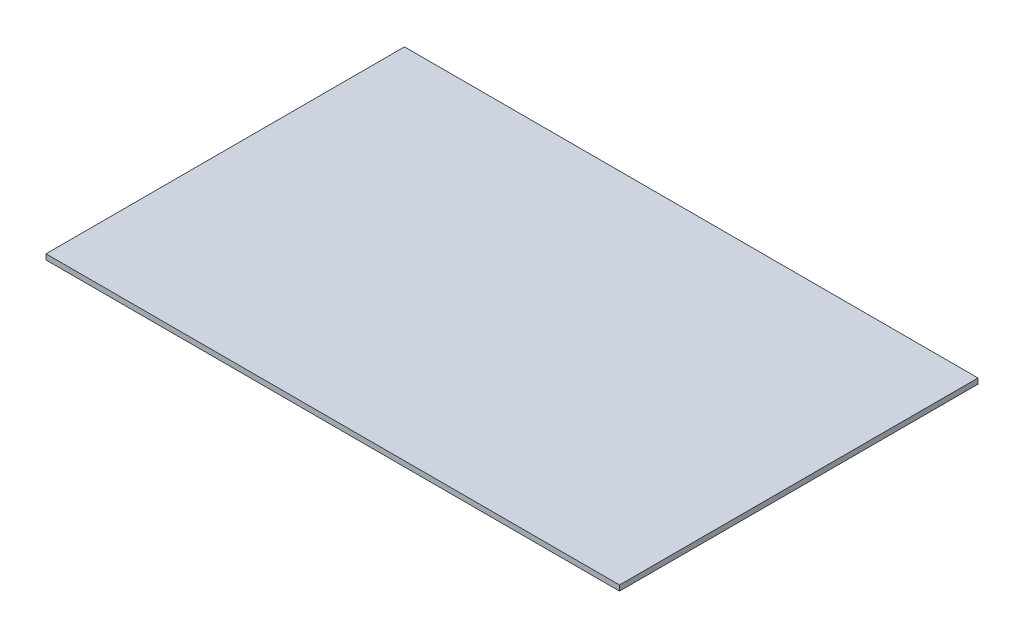
SolidWorks part; units mm, degrees
ref_plane "Спереди" through (0, 0, 0) normal (0, 0, 1) x (1, 0, 0)
ref_plane "Сверху" through (0, 0, 0) normal (0, 1, 0) x (1, 0, 0)
ref_plane "Справа" through (0, 0, 0) normal (1, 0, 0) x (0, 0, -1)
sketch "Эскиз1" plane through (0, 0, 0) normal (0, 1, 0) x (1, 0, 0)
  line L1 (-80, 50) -> (80, 50)
  line L2 (-80, 50) -> (-80, -50)
  line L3 (-80, -50) -> (80, -50)
  line L4 (80, 50) -> (80, -50)
  line L5 (-80, 50) -> (80, -50) construction
  line L6 (-80, -50) -> (80, 50) construction
  point P0 (0, 0)
extrude "Бобышка-Вытянуть1" add sketch "Эскиз1" along normal blind 1.5
